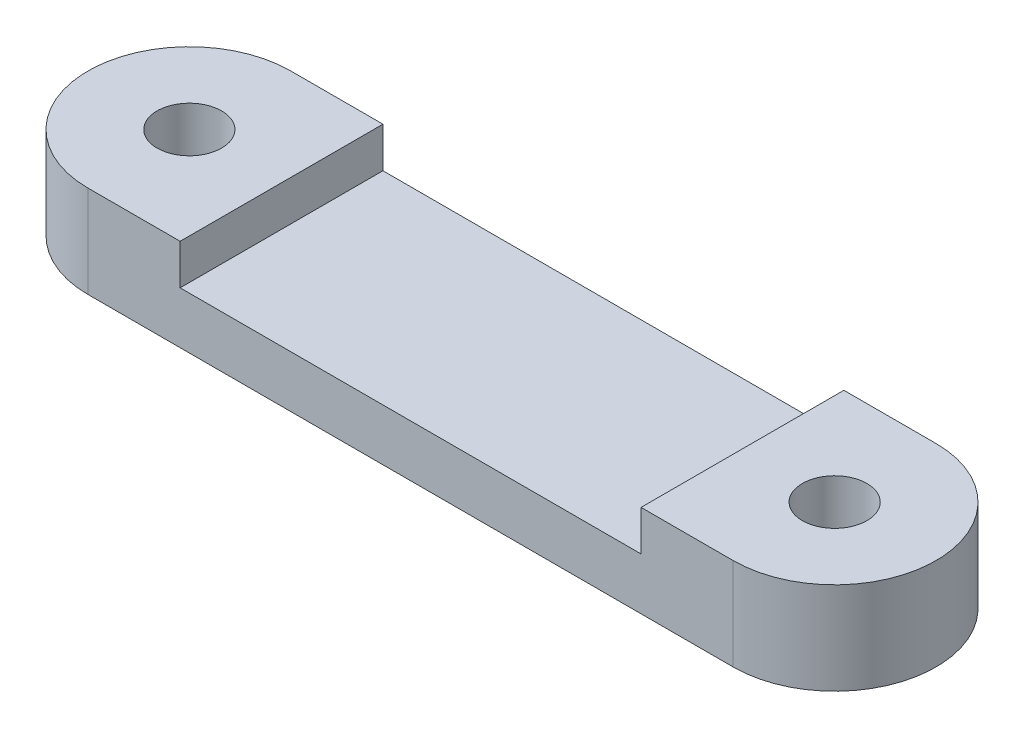
SolidWorks part; units mm, degrees
ref_plane "Front Plane" through (0, 0, 0) normal (0, 0, 1) x (1, 0, 0)
ref_plane "Top Plane" through (0, 0, 0) normal (0, 1, 0) x (1, 0, 0)
ref_plane "Right Plane" through (0, 0, 0) normal (1, 0, 0) x (0, 0, -1)
sketch "Sketch1" plane through (0, 0, 0) normal (0, 1, 0) x (1, 0, 0)
  line L0 (0, 4.4) -> (28, 4.4) construction
  line L1 (0, 0) -> (28, 0)
  line L3 (0, 8.8) -> (28, 8.8)
  line L5 (0, 8.8) -> (0, 0) construction
  line L6 (28, 8.8) -> (28, 0) construction
  circle A0 centre (0, 4.4) radius 1.4
  circle A1 centre (28, 4.4) radius 1.4
  arc A2 (0, 8.8) -> (0, 0) centre (0, 4.4) ccw
  arc A3 (28, 8.8) -> (28, 0) centre (28, 4.4) cw
  point P12 (28, 4.4)
  dimension "D1" = 2.8
  dimension "D2" = 3
  dimension "D3" = 28
extrude "Boss-Extrude1" add sketch "Sketch1" along normal blind 4
sketch "Sketch2" plane through (0, 4, 0) normal (0, 1, 0) x (1, 0, 0)
  line L0 (0, 0) -> (28, 0) construction
  line L1 (24, 0) -> (4, 0)
  line L2 (24, 0) -> (24, 8.8)
  line L3 (24, 8.8) -> (4, 8.8)
  line L4 (4, 0) -> (4, 8.8)
  line L5 (0, 8.8) -> (28, 8.8) construction
  line L6 (28, 8.8) -> (28, 0) construction
  line L7 (0, 8.8) -> (0, 0) construction
  dimension "D1" = 4
  dimension "D2" = 4
extrude "Cut-Extrude1" cut sketch "Sketch2" against normal blind 1.75
